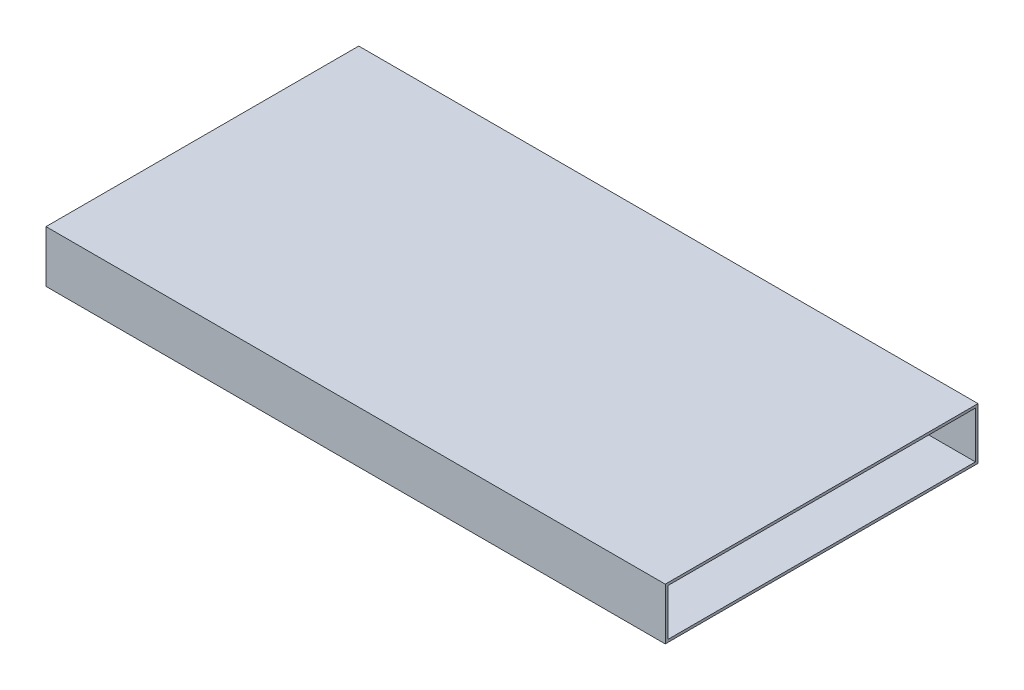
SolidWorks part; units mm, degrees
ref_plane "Alzado" through (0, 0, 0) normal (0, 0, 1) x (1, 0, 0)
ref_plane "Planta" through (0, 0, 0) normal (0, 1, 0) x (1, 0, 0)
ref_plane "Vista lateral" through (0, 0, 0) normal (1, 0, 0) x (0, 0, -1)
sketch "Croquis1" plane through (0, 0, 0) normal (0, 1, 0) x (1, 0, 0)
  line L1 (0, 0) -> (-119.5372, 0)
  line L2 (0, 0) -> (0, -60.3703)
  line L3 (0, -60.3703) -> (-119.5372, -60.3703)
  line L4 (-119.5372, 0) -> (-119.5372, -60.3703)
extrude "Saliente-Extruir1" add sketch "Croquis1" along normal blind 10
shell "Vaciado1" thickness 0.5
